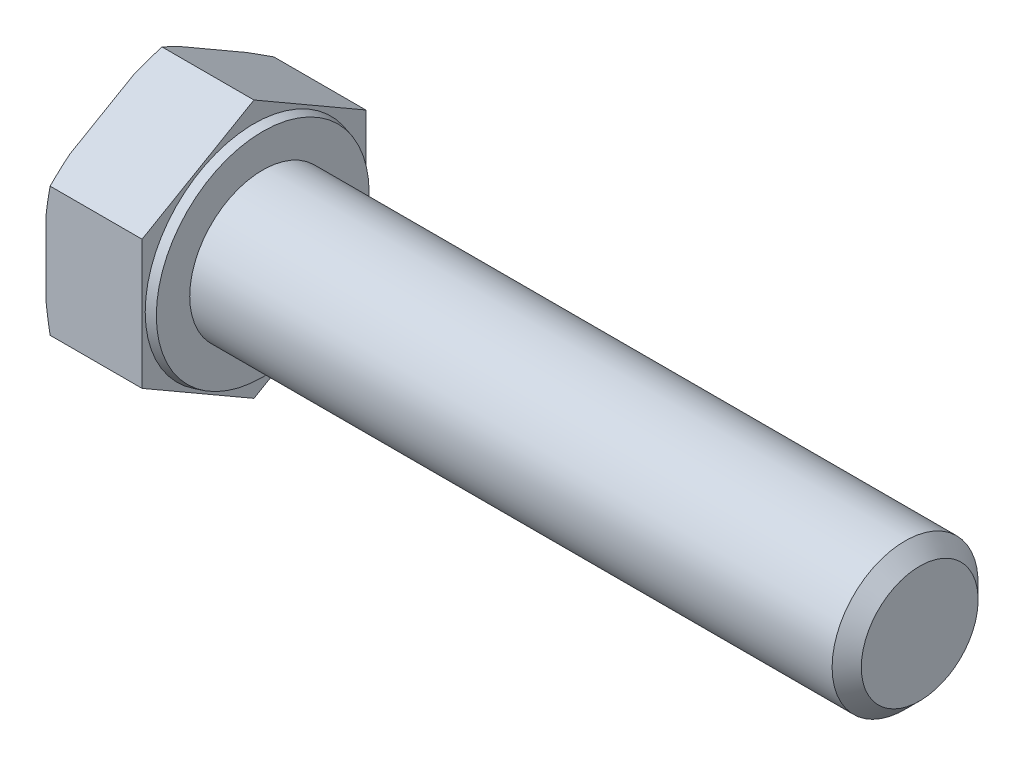
SolidWorks part; units mm, degrees
material "AISI 1020"
ref_plane "Спереди" through (0, 0, 0) normal (0, 0, 1) x (1, 0, 0)
ref_plane "Сверху" through (0, 0, 0) normal (0, 1, 0) x (1, 0, 0)
ref_plane "Справа" through (0, 0, 0) normal (1, 0, 0) x (0, 0, -1)
sketch "Эскиз1" plane through (0, 0, 0) normal (0, 0, 1) x (1, 0, 0)
  line L0 (-1000, 0) -> (49000, 0) construction
  line L1 (-6.58, 0) -> (-6.58, 8.85)
  line L2 (-6.58, 8.85) -> (0, 8.85)
  line L3 (0, 8.85) -> (0, 7.449)
  line L4 (0.6, 5) -> (45.6, 5)
  line L5 (45.6, 5) -> (45.6, 0)
  line L6 (-6.58, 0) -> (45.6, 0)
  line L7 (0, 7.449) -> (0.6, 7.2882)
  line L8 (0.6, 7.2882) -> (0.6, 5)
  line L9 (0.5, 0) -> (0.5, 7.315) construction
  dimension "_d" = 10
  dimension "D1" = 45
  dimension "D5" = 17.7
  dimension "D2" = 0.6
  dimension "D3" = 6.58
  dimension "D4" = 0.1
  dimension "D6" = 14.63
  dimension "D7" = 75
revolve "Повернуть1" add sketch "Эскиз1" angle 360 about L0
sketch "Эскиз2" plane through (-6.58, 0, 0) normal (-1, 0, 0) x (0, 0, 1)
  line L1 (0, -8.85) -> (7.6643, -4.425)
  line L2 (7.6643, -4.425) -> (7.6643, 4.425)
  line L3 (7.6643, 4.425) -> (0, 8.85)
  line L4 (0, 8.85) -> (-7.6643, 4.425)
  line L5 (-7.6643, 4.425) -> (-7.6643, -4.425)
  line L6 (-7.6643, -4.425) -> (0, -8.85)
  circle A0 centre (0, 0) radius 7.6643 construction
  circle A1 centre (0, 0) radius 8.85 construction
extrude "Вырез-Вытянуть1" cut sketch "Эскиз2" against normal through all flip side to cut
sketch "Эскиз4" plane through (0, 0, 0) normal (0, 0, 1) x (1, 0, 0)
  line L0 (-1000, 0) -> (49000, 0) construction
  line L1 (-6.58, 8.075) -> (-6.2979, 8.85)
  line L2 (-6.2979, 8.85) -> (-6.58, 8.85)
  line L3 (-6.58, 8.85) -> (-6.58, 8.075)
  line L4 (-6.58, 4.425) -> (-6.58, 8.85) construction
  line L6 (0, 8.85) -> (-6.58, 8.85) construction
  dimension "D1" = 20
  dimension "D2" = 16.15
revolve "Вырез-Повернуть1" cut sketch "Эскиз4" angle 360 about L0
chamfer "Фаска1" distance 1 angle 45 1 edges at (45.6, 0, 5)
equation "\"l\"= 45'длина болта"
equation "\"_d\"= 10'диаметр болта"
equation "\"b\"= 20'длина резьбы"
equation "\"k\"= 6.58'толщина шляпки"
equation "\"e\"= 17.7'диаметр головки описанный"
equation "\"S\"= 17'размер под ключ"
equation "\"_d@Эскиз1\"=\"_d\""
equation "\"dw\"= 14.63"
equation "\"da\"= 9.78"
equation "\"с\"= 0.6"
equation "\"D1@Эскиз1\"=\"l\""
equation "\"D5@Эскиз1\"=\"e\""
equation "\"D2@Эскиз1\"=\"с\""
equation "\"D3@Эскиз1\"=\"k\""
equation "\"D2@Эскиз4\"=\"S\"*0.95"
equation "\"D1@Фаска1\"=\"_d\"/10"
equation "\"D6@Эскиз1\"=\"dw\""
